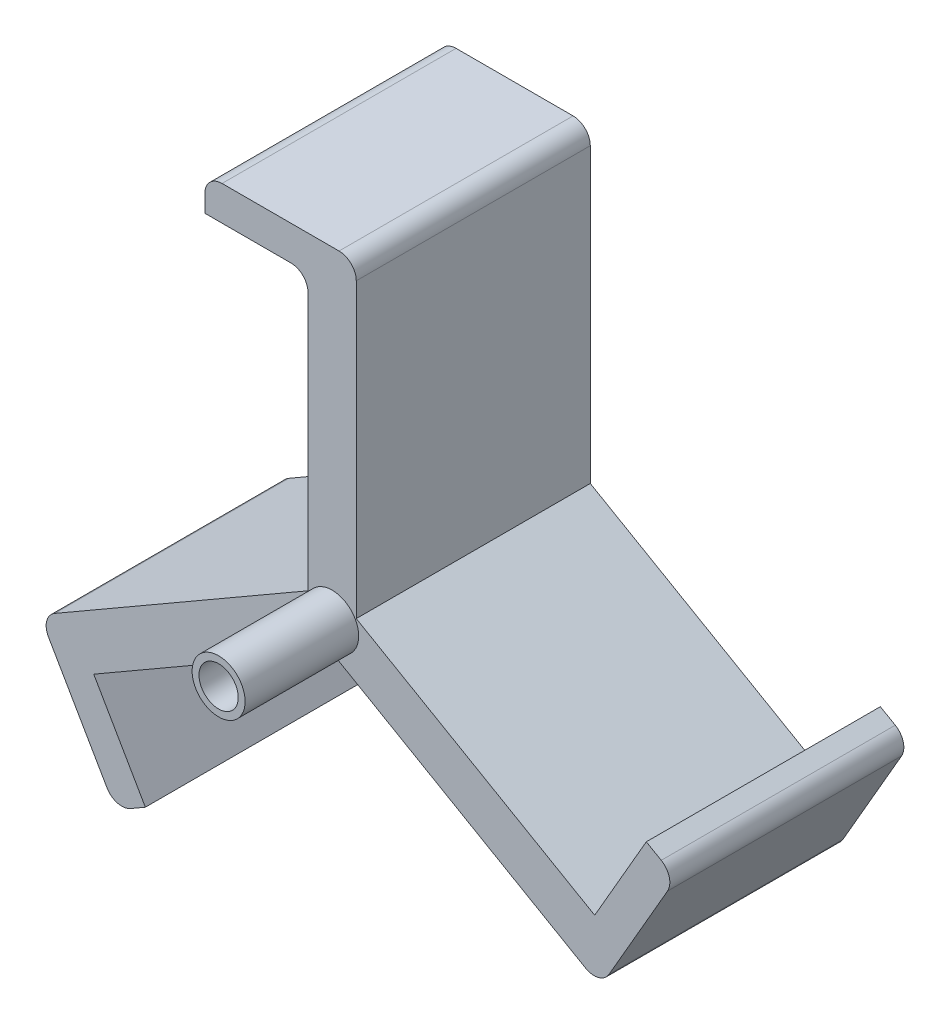
SolidWorks part; units mm, degrees
ref_plane "前基準面" through (0, 0, 0) normal (0, 0, 1) x (1, 0, 0)
ref_plane "上基準面" through (0, 0, 0) normal (0, 1, 0) x (1, 0, 0)
ref_plane "右基準面" through (0, 0, 0) normal (1, 0, 0) x (0, 0, -1)
sketch "草圖1" plane through (0, 0, 0) normal (0, 0, 1) x (1, 0, 0)
  line L24 (0.5912, -5.4419) -> (39.5624, -27.9419)
  line L25 (39.5624, -27.9419) -> (36.0624, -34.0041)
  line L26 (36.0624, -34.0041) -> (-2.9088, -11.5041)
  line L27 (-2.9088, -11.5041) -> (-41.8799, -34.0041)
  line L28 (-41.8799, -34.0041) -> (-45.3799, -27.9419)
  line L29 (-45.3799, -27.9419) -> (-6.4088, -5.4419)
  line L30 (-6.4088, -5.4419) -> (-6.4088, 39.5581)
  line L31 (-6.4088, 39.5581) -> (0.5912, 39.5581)
  line L32 (0.5912, 39.5581) -> (0.5912, -5.4419)
  line L33 (-6.4088, -5.4419) -> (0.5912, -5.4419) construction
  line L34 (-6.4088, -5.4419) -> (-2.9088, -11.5041) construction
  line L35 (-2.9088, -11.5041) -> (0.5912, -5.4419) construction
  line L36 (-6.4088, -5.4419) -> (-2.2838, -7.8235) construction
  line L37 (-4.6588, -8.473) -> (0.5912, -5.4419) construction
  line L38 (-2.9088, -5.4419) -> (-2.9088, -11.5041) construction
  point P12 (-2.9088, -7.4626)
  dimension "D1" = 45
  dimension "D2" = 45
  dimension "D3" = 90
  dimension "D4" = 7
  dimension "D5" = 7
  dimension "D6" = 7
  dimension "D7" = 45
  dimension "D8" = 45
  dimension "D9" = 45
  dimension "D10" = 45
extrude "填料-伸長1" add sketch "草圖1" along normal blind 34
sketch "草圖4" plane through (0, 0, 34) normal (0, 0, 1) x (1, 0, 0)
  circle A1 centre (-2.9088, -7.4626) radius 2.85
  circle A2 centre (-2.9088, -7.4626) radius 3.85
  point P7 (-2.9088, -7.5931)
  dimension "D1" = 5.7
  dimension "D2" = 7.7
extrude "填料-伸長2" add sketch "草圖4" along normal blind 16.5
sketch "草圖5" plane through (0, 0, 34) normal (0, 0, 1) x (1, 0, 0)
  circle A0 centre (-2.9088, -7.4626) radius 1.85
  dimension "D1" = 3.7
extrude "除料-伸長2" cut sketch "草圖5" against normal through all
sketch "草圖6" plane through (0, 0, 0) normal (0, 0, -1) x (-1, 0, 0)
  circle A0 centre (2.9088, -7.4626) radius 3
  dimension "D1" = 6
extrude "除料-伸長3" cut sketch "草圖6" against normal blind 4
sketch "草圖7" plane through (-6.4088, 0, 0) normal (-1, 0, 0) x (0, 0, 1)
  line L0 (34, 39.5581) -> (34, -5.4419) construction
  line L1 (0, 39.5581) -> (34, 39.5581)
  line L2 (0, 39.5581) -> (0, 34.5581)
  line L3 (0, 34.5581) -> (34, 34.5581)
  line L4 (34, 39.5581) -> (34, 34.5581)
  dimension "D1" = 5
extrude "填料-伸長3" add sketch "草圖7" along normal blind 15
fillet "圓角2" radius 2.5 1 edges at (-21.4088, 39.5581, 17)
fillet "圓角3" radius 2.5 1 edges at (0.5912, 39.5581, 17)
fillet "圓角4" radius 2.5 1 edges at (-6.4088, 34.5581, 17)
sketch "草圖8" plane through (4.2542, -7.3685, 0) normal (0.5, -0.866, 0) x (0.866, 0.5, 0)
  line L0 (-53.2711, 34) -> (-8.2711, 34) construction
  line L1 (-53.2711, 0) -> (-48.2711, 0)
  line L2 (-53.2711, 0) -> (-53.2711, 34)
  line L3 (-53.2711, 34) -> (-48.2711, 34)
  line L4 (-48.2711, 0) -> (-48.2711, 34)
  dimension "D1" = 5
extrude "填料-伸長4" add sketch "草圖8" along normal blind 15
sketch "草圖9" plane through (-2.2086, -3.8254, 0) normal (0.5, 0.866, 0) x (0.866, -0.5, 0)
  line L0 (48.233, 0) -> (3.233, 0) construction
  line L1 (48.233, -34) -> (43.233, -34)
  line L2 (48.233, -34) -> (48.233, 0)
  line L3 (48.233, 0) -> (43.233, 0)
  line L4 (43.233, -34) -> (43.233, 0)
  dimension "D1" = 5
extrude "填料-伸長5" add sketch "草圖9" along normal blind 15
fillet "圓角5" radius 2.5 4 edges at (47.0624, -14.9515, 17) (36.0624, -34.0041, 17) (-45.3799, -27.9419, 17) (-34.3799, -46.9945, 17)
